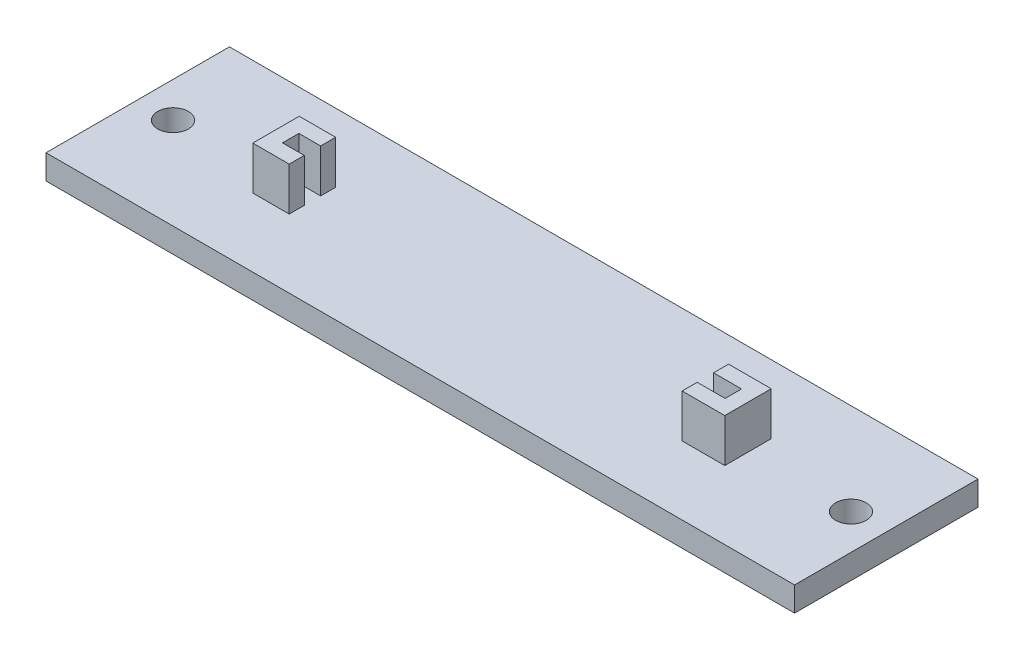
SolidWorks part; units mm, degrees
ref_plane "Front Plane" through (0, 0, 0) normal (0, 0, 1) x (1, 0, 0)
ref_plane "Top Plane" through (0, 0, 0) normal (0, 1, 0) x (1, 0, 0)
ref_plane "Right Plane" through (0, 0, 0) normal (1, 0, 0) x (0, 0, -1)
sketch "Sketch1" plane through (0, 0, 0) normal (0, 1, 0) x (1, 0, 0)
  line L1 (-38.875, 9.525) -> (38.875, 9.525)
  line L2 (-38.875, 9.525) -> (-38.875, -9.525)
  line L3 (-38.875, -9.525) -> (38.875, -9.525)
  line L4 (38.875, 9.525) -> (38.875, -9.525)
  line L5 (-38.875, 9.525) -> (38.875, -9.525) construction
  line L6 (-38.875, -9.525) -> (38.875, 9.525) construction
  point P0 (0, 0)
  dimension "D1" = 19.05
  dimension "D2" = 77.75
extrude "Boss-Extrude1" add sketch "Sketch1" along normal blind 2.54
sketch "Sketch2" plane through (0, 2.54, 0) normal (0, 1, 0) x (1, 0, 0)
  line L0 (38.875, 0) -> (36.7922, 0) construction
  line L1 (38.875, -9.525) -> (38.875, 9.525) construction
  line L2 (36.7922, 0) -> (35.2047, 0) construction
  line L3 (-38.875, 0) -> (-36.7922, 0) construction
  line L4 (-38.875, 9.525) -> (-38.875, -9.525) construction
  line L5 (-36.7922, 0) -> (-35.2047, 0) construction
  circle A0 centre (35.2047, 0) radius 1.5875
  circle A1 centre (-35.2047, 0) radius 1.5875
  dimension "D1" = 2.0828
  dimension "D2" = 1.5875
  dimension "D3" = 2.0828
  dimension "D4" = 1.5875
extrude "Cut-Extrude1" cut sketch "Sketch2" against normal through all
sketch "Sketch3" plane through (0, 2.54, 0) normal (0, 1, 0) x (1, 0, 0)
  line L1 (-24.511, 2.413) -> (24.511, 2.413)
  line L2 (-24.511, 2.413) -> (-24.511, -2.413)
  line L3 (-24.511, -2.413) -> (24.511, -2.413)
  line L4 (24.511, 2.413) -> (24.511, -2.413)
  line L5 (-24.511, 2.413) -> (24.511, -2.413) construction
  line L6 (-24.511, -2.413) -> (24.511, 2.413) construction
  point P0 (0, 0)
  dimension "D1" = 49.022
  dimension "D2" = 4.826
extrude "Boss-Extrude2" add sketch "Sketch3" along normal blind 4.4958
sketch "Sketch4" plane through (0, 7.0358, 0) normal (0, 1, 0) x (1, 0, 0)
  line L0 (-22.733, -2.413) -> (-20.7264, -2.413) construction
  line L1 (-22.987, 0.8509) -> (22.987, 0.8509)
  line L2 (-22.987, 0.8509) -> (-22.987, -0.8509)
  line L3 (-22.987, -0.8509) -> (22.987, -0.8509)
  line L4 (22.987, 0.8509) -> (22.987, -0.8509)
  line L5 (-22.987, 0.8509) -> (22.987, -0.8509) construction
  line L6 (-22.987, -0.8509) -> (22.987, 0.8509) construction
  line L7 (-24.511, -2.413) -> (24.511, -2.413) construction
  line L8 (-24.511, -2.413) -> (24.511, -2.413) construction
  line L9 (22.091, -2.413) -> (20.0844, -2.413) construction
  point P0 (0, 0)
  dimension "D1" = 45.974
  dimension "D2" = 1.7018
  dimension "D3" = 2.0066
  dimension "D4" = 2.0066
extrude "Cut-Extrude2" cut sketch "Sketch4" against normal blind 4.4958
sketch "Sketch6" plane through (0, 7.0358, 0) normal (0, 1, 0) x (1, 0, 0)
  line L0 (-20.7264, -2.413) -> (-20.7264, -0.8509)
  line L1 (-22.987, -0.8509) -> (22.987, -0.8509) construction
  line L2 (-20.7264, -2.413) -> (20.0844, -2.413)
  line L3 (20.0844, -2.413) -> (20.0844, -0.8509)
  line L4 (20.0844, -0.8509) -> (-20.7264, -0.8509)
  line L5 (-20.7264, 0.8509) -> (-20.7264, 2.413)
  line L6 (-22.987, 0.8509) -> (22.987, 0.8509) construction
  line L7 (24.511, 2.413) -> (-24.511, 2.413) construction
  line L8 (-20.7264, 2.413) -> (20.0844, 2.413)
  line L9 (20.0844, 2.413) -> (20.0844, 0.8509)
  line L10 (20.0844, 0.8509) -> (-20.7264, 0.8509)
extrude "Cut-Extrude3" cut sketch "Sketch6" against normal blind 4.4958
